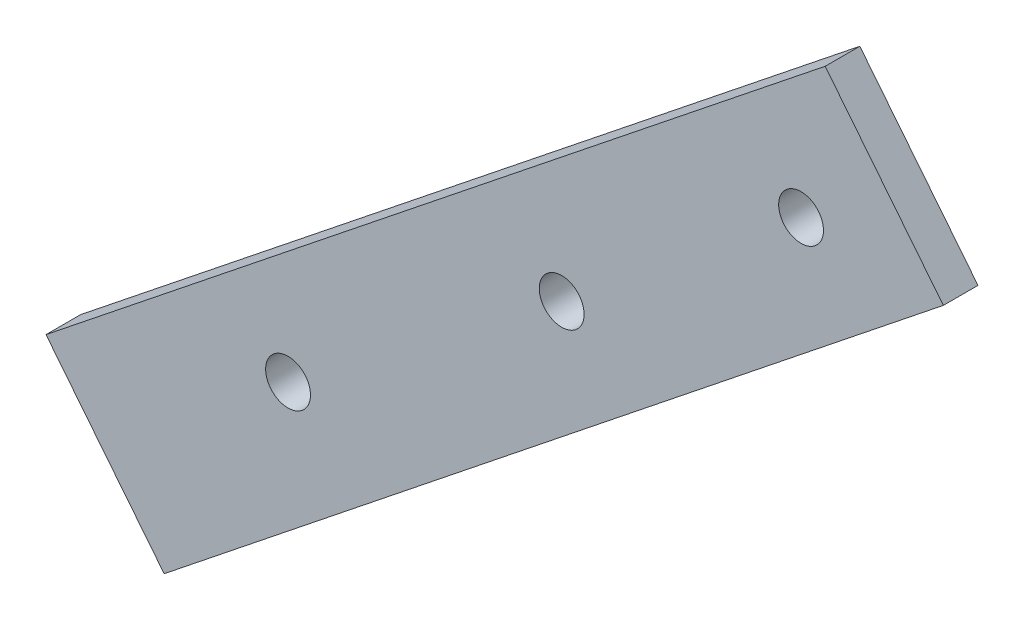
SolidWorks part; units mm, degrees
ref_plane "Front" through (0, 0, 0) normal (0, 0, 1) x (1, 0, 0)
ref_plane "Top" through (0, 0, 0) normal (0, 1, 0) x (1, 0, 0)
ref_plane "Right" through (0, 0, 0) normal (1, 0, 0) x (0, 0, -1)
sketch "Sketch1" plane through (0, 0, 0) normal (0, 0, 1) x (1, 0, 0)
  line L0 (0, 0) -> (-34.0944, 42.712)
  line L1 (-34.0944, 42.712) -> (190.731, 222.1764)
  line L2 (190.731, 222.1764) -> (224.8254, 179.4644)
  line L3 (224.8254, 179.4644) -> (0, 0)
  circle A0 centre (35.7432, 65.7604) radius 6.47
  circle A1 centre (114.6982, 125.4114) radius 6.47
  circle A2 centre (183.7696, 180.9069) radius 6.47
extrude "Boss-Extrude1" add sketch "Sketch1" along normal blind 10
sketch "Sketch3"
  circle A0 centre (-35.7432, 65.7604) radius 6.47 construction
  circle A1 centre (-114.6982, 125.4114) radius 6.47 construction
  circle A2 centre (-183.7696, 180.9069) radius 6.47 construction
other "AlignGroup1" parameters "D1"=0, "D2"=35.7432, "D3"=114.6982, "D4"=183.7696, "D5"=0
other "AlignGroup2"
